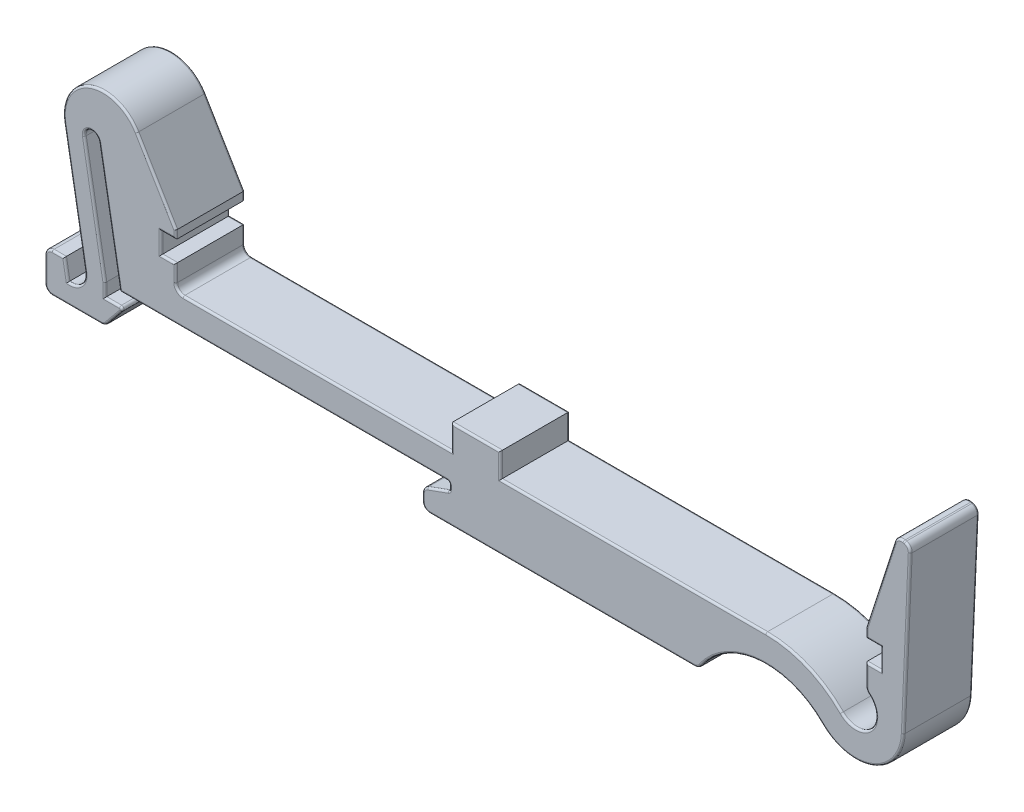
SolidWorks part; units mm, degrees
ref_plane "Front Plane" through (0, 0, 0) normal (0, 0, 1) x (1, 0, 0)
ref_plane "Top Plane" through (0, 0, 0) normal (0, 1, 0) x (1, 0, 0)
ref_plane "Right Plane" through (0, 0, 0) normal (1, 0, 0) x (0, 0, -1)
sketch "Sketch1" plane through (0, 0, 0) normal (0, 0, 1) x (1, 0, 0)
  line L0 (-6.797, 0.2) -> (-8.047, 0.2)
  line L1 (-6.797, 0.2) -> (-6.4443, -1.8)
  line L2 (-8.797, -0.55) -> (-8.797, -3.05)
  line L3 (-8.047, -3.8) -> (-3.0764, -3.8)
  line L4 (-2.4964, -3.5255) -> (-1.0067, -1.7085)
  line L6 (-1.2, -1.3) -> (-2.7, -1.3)
  line L7 (-2.7, -1.3) -> (-2.7, 0)
  line L8 (-2.7, 0) -> (-4.7838, 11.8177)
  line L9 (-3.3066, 12.0782) -> (-1.1769, 0)
  line L10 (-1.1769, 0) -> (32.05, 0)
  line L13 (32.3, -0.25) -> (32.3, -0.6249)
  line L14 (32.1355, -0.8599) -> (30.0435, -1.6213)
  line L15 (29.55, -2.3261) -> (29.55, -3.0509)
  line L16 (30.3, -3.8009) -> (57.195, -3.8009)
  line L17 (78.4091, 0.8288) -> (79.1111, 17.0699)
  line L18 (77.505, 17.3718) -> (74.6, 8.3666)
  line L19 (74.6, 8.3666) -> (74.6, 7.4)
  line L20 (74.6, 7.4) -> (76.1, 7.4)
  line L21 (76.1, 7.4) -> (76.1, 5.3)
  line L22 (76.1, 5.3) -> (74.6, 5.3)
  line L23 (74.6, 5.3) -> (74.6, 3.1885)
  line L24 (64.4362, 2.8) -> (5.25, 2.8)
  line L25 (4.5, 3.55) -> (4.5, 5.3)
  line L26 (4.5, 5.3) -> (3, 5.3)
  line L27 (3, 5.3) -> (3, 7.4)
  line L28 (3, 7.4) -> (4.5, 7.4)
  line L29 (4.5, 7.4) -> (4.5, 8.2271)
  line L30 (4.5, 8.2271) -> (0.5556, 14.8347)
  line L31 (-6.8599, 12.0743) -> (-4.7309, 0)
  line L35 (78.4118, 17.8654) -> (78.5559, 17.8268)
  arc A0 (-8.047, 0.2) -> (-8.797, -0.55) centre (-8.047, -0.55) ccw
  arc A1 (-8.797, -3.05) -> (-8.047, -3.8) centre (-8.047, -3.05) ccw
  arc A2 (-3.0764, -3.8) -> (-2.4964, -3.5255) centre (-3.0764, -3.05) ccw
  arc A3 (-1.0067, -1.7085) -> (-1.2, -1.3) centre (-1.2, -1.55) ccw
  arc A4 (-4.7838, 11.8177) -> (-3.3066, 12.0782) centre (-4.0452, 11.9479) cw
  arc A5 (32.05, 0) -> (32.3, -0.25) centre (32.05, -0.25) cw
  arc A6 (32.3, -0.6249) -> (32.1355, -0.8599) centre (32.05, -0.6249) cw
  arc A7 (30.0435, -1.6213) -> (29.55, -2.3261) centre (30.3, -2.3261) ccw
  arc A8 (29.55, -3.0509) -> (30.3, -3.8009) centre (30.3, -3.0509) ccw
  arc A9 (57.195, -3.8009) -> (57.8123, -3.4769) centre (57.195, -3.0509) ccw
  arc A10 (57.8123, -3.4769) -> (70.1435, -2.3738) centre (64.4362, -8.0481) cw
  arc A11 (70.1435, -2.3738) -> (78.4091, 0.8288) centre (73.5749, 1.0378) ccw
  arc A12 (79.1111, 17.0699) -> (78.5559, 17.8268) centre (78.3618, 17.1023) ccw
  arc A13 (78.4118, 17.8654) -> (77.505, 17.3718) centre (78.2179, 17.1418) ccw
  arc A14 (74.6, 3.1885) -> (74.8726, 2.6101) centre (75.35, 3.1885) ccw
  arc A15 (74.8726, 2.6101) -> (72.1291, -0.3996) centre (73.5749, 1.0378) cw
  arc A16 (64.4362, 2.8) -> (72.1291, -0.3996) centre (64.4362, -8.0481) cw
  arc A17 (5.25, 2.8) -> (4.5, 3.55) centre (5.25, 3.55) cw
  arc A18 (0.5556, 14.8347) -> (-6.8599, 12.0743) centre (-2.8984, 12.7728) ccw
  arc A19 (-4.7309, 0) -> (-6.4443, -1.8) centre (-6.2514, -0.2681) cw
  dimension "D1" = 35
  dimension "D2" = 73.1
  dimension "D3" = 1.5
extrude "Boss-Extrude1" add sketch "Sketch1" along normal blind 7
sketch "Sketch2" plane through (0, 0, 0) normal (0, 0, 1) x (1, 0, 0)
  line L1 (32.5, 2.8) -> (37.5, 2.8)
  line L2 (32.5, 2.8) -> (32.5, 5.3)
  line L3 (32.5, 5.3) -> (37.5, 5.3)
  line L4 (37.5, 2.8) -> (37.5, 5.3)
  line L5 (64.4362, 2.8) -> (5.25, 2.8) construction
  line L6 (4.5, 5.3) -> (3, 5.3) construction
  line L7 (3, 6.35) -> (76.1, 6.35) construction
  line L8 (3, 5.3) -> (3, 7.4) construction
  line L9 (76.1, 7.4) -> (76.1, 5.3) construction
  line L10 (39.55, 6.35) -> (39.55, 5.3) construction
  point P4 (35, 5.3)
  dimension "D1" = 5
  dimension "D2" = 32
extrude "Boss-Extrude2" add sketch "Sketch2" along normal up to surface (7 mm away) up to face at (28.7528, 3.2793, 7)
fillet "Fillet1" radius 0.2 108 edges at (-7.422, 0.2, 0) (-8.5773, -0.0197, 0) (-8.797, -1.8, 0) (-8.5773, -3.5803, 0) (-5.5617, -3.8, 0) (-2.7556, -3.7279, 0) (-1.7515, -2.617, 0) (-0.974, -1.4431, 0) (-1.95, -1.3, 0) (-2.7, -0.65, 0) (-3.7419, 5.9088, 0) (-4.1754, 12.6865, 0) (-2.2417, 6.0391, 0) (15.4366, 0, 0) (32.2268, -0.0732, 0) (32.3, -0.4375, 0) (32.2548, -0.7683, 0) (31.0895, -1.2406, 0) (29.6856, -1.8959, 0) (29.55, -2.6885, 0) (29.7697, -3.5812, 0) (43.7475, -3.8009, 0) (57.5436, -3.715, 0) (63.7191, -0.032, 0) (75.3231, -3.4741, 0) (78.7601, 8.9494, 0) (78.9665, 17.5459, 0) (78.4838, 17.8461, 0) (77.8598, 17.7998, 0) (76.0525, 12.8692, 0) (74.6, 7.8833, 0) (75.35, 7.4, 0) (76.1, 6.35, 0) (75.35, 5.3, 0) (74.6, 4.2443, 0) (74.6716, 2.8688, 0) (75.0816, -0.3356, 0) (68.6021, 1.9682, 0) (18.875, 2.8, 0) (50.9681, 2.8, 0) (4.7197, 3.0197, 0) (4.5, 4.425, 0) (3.75, 5.3, 0) (3, 6.35, 0) (3.75, 7.4, 0) (4.5, 7.8136, 0) (2.5278, 11.5309, 0) (-4.3017, 16.5427, 0) (-5.7954, 6.0372, 0) (-5.1331, -1.3327, 0) (-6.6206, -0.8, 0) (-5.1331, -1.3327, 7) (-5.7954, 6.0372, 7) (-4.3017, 16.5427, 7) (2.5278, 11.5309, 7) (4.5, 7.8136, 7) (3.75, 7.4, 7) (3, 6.35, 7) (3.75, 5.3, 7) (4.5, 4.425, 7) (4.7197, 3.0197, 7) (50.9681, 2.8, 7) (18.875, 2.8, 7) (68.6021, 1.9682, 7) (75.0816, -0.3356, 7) (74.6716, 2.8688, 7) (74.6, 4.2443, 7) (75.35, 5.3, 7) (76.1, 6.35, 7) (75.35, 7.4, 7) (74.6, 7.8833, 7) (76.0525, 12.8692, 7) (77.8598, 17.7998, 7) (78.4838, 17.8461, 7) (78.9665, 17.5459, 7) (78.7601, 8.9494, 7) (75.3231, -3.4741, 7) (63.7191, -0.032, 7) (57.5436, -3.715, 7) (43.7475, -3.8009, 7) (29.7697, -3.5812, 7) (29.55, -2.6885, 7) (29.6856, -1.8959, 7) (31.0895, -1.2406, 7) (32.2548, -0.7683, 7) (32.3, -0.4375, 7) (32.2268, -0.0732, 7) (15.4366, 0, 7) (-2.2417, 6.0391, 7) (-4.1754, 12.6865, 7) (-3.7419, 5.9088, 7) (-2.7, -0.65, 7) (-1.95, -1.3, 7) (-0.974, -1.4431, 7) (-1.7515, -2.617, 7) (-2.7556, -3.7279, 7) (-5.5617, -3.8, 7) (-8.5773, -3.5803, 7) (-8.797, -1.8, 7) (-8.5773, -0.0197, 7) (-7.422, 0.2, 7) (-6.6206, -0.8, 7) (37.5, 4.05, 7) (37.5, 4.05, 0) (35, 5.3, 7) (35, 5.3, 0) (32.5, 4.05, 7) (32.5, 4.05, 0)
